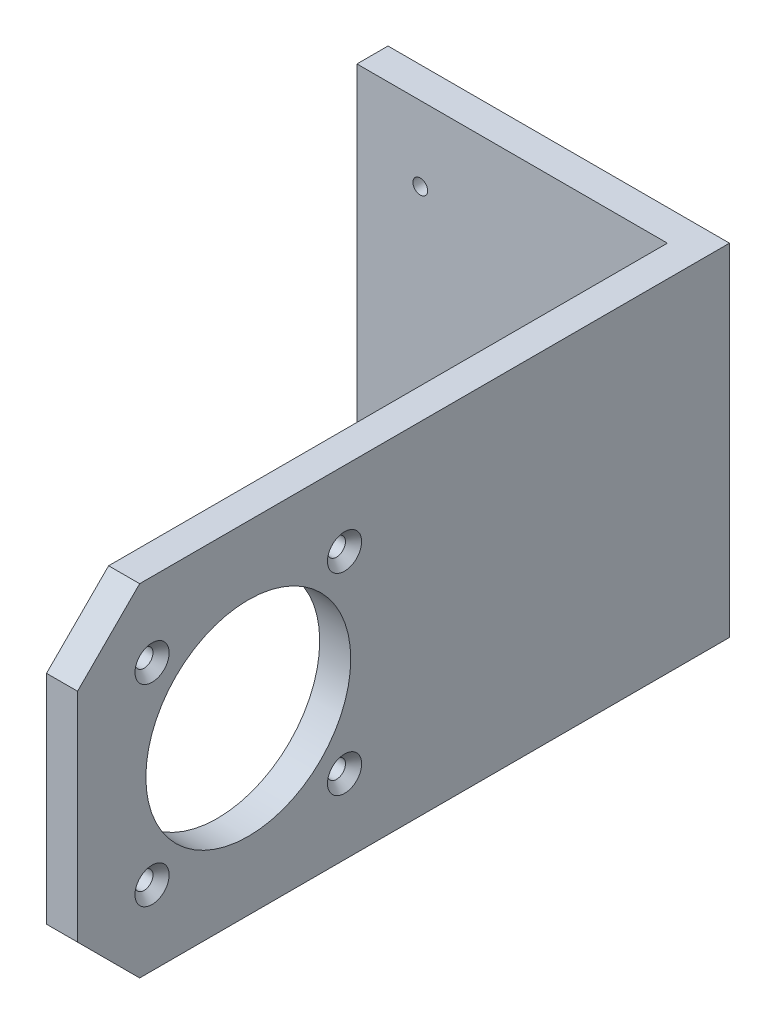
SolidWorks part; units mm, degrees
ref_plane "Ön Düzlem" through (0, 0, 0) normal (0, 0, 1) x (1, 0, 0)
ref_plane "Üst Düzlem" through (0, 0, 0) normal (0, 1, 0) x (1, 0, 0)
ref_plane "Sağ Düzlem" through (0, 0, 0) normal (1, 0, 0) x (0, 0, -1)
sketch "Sketch1" plane through (0, 0, 0) normal (0, 0, 1) x (1, 0, 0)
  line L1 (-27.5, 27.5) -> (27.5, 27.5)
  line L2 (-27.5, 27.5) -> (-27.5, -27.5)
  line L3 (-27.5, -27.5) -> (27.5, -27.5)
  line L4 (27.5, 27.5) -> (27.5, -27.5)
  line L5 (-27.5, 27.5) -> (27.5, -27.5) construction
  line L6 (-27.5, -27.5) -> (27.5, 27.5) construction
  point P0 (0, 0)
  dimension "D1" = 55
  dimension "D2" = 55
extrude "Boss-Extrude1" add sketch "Sketch1" along normal blind 5
sketch "Sketch2" plane through (0, 0, 5) normal (0, 0, 1) x (1, 0, 0)
  line L0 (-27.5, -27.5) -> (27.5, -27.5) construction
  line L1 (27.5, 27.5) -> (22.5, 27.5)
  line L2 (27.5, 27.5) -> (27.5, -27.5)
  line L3 (27.5, -27.5) -> (22.5, -27.5)
  line L4 (22.5, 27.5) -> (22.5, -27.5)
  dimension "D1" = 5
extrude "Boss-Extrude2" add sketch "Sketch2" along normal blind 100
sketch "Sketch3" plane through (27.5, 0, 0) normal (1, 0, 0) x (0, 0, -1)
  line L0 (-105, -27.5) -> (-105, 27.5) construction
  circle A0 centre (-77.5, 0) radius 16.5
  point P2 (-105, 0)
  dimension "D1" = 33
  dimension "D2" = 27.5
extrude "Cut-Extrude1" cut sketch "Sketch3" against normal up to next
sketch "Sketch4" plane through (0, 0, 5) normal (0, 0, 1) x (1, 0, 0)
  circle A0 centre (0, 0) radius 2.5
  dimension "D1" = 5
extrude "Cut-Extrude2" cut sketch "Sketch4" against normal up to next
sketch "Sketch5" plane through (27.5, 0, 0) normal (1, 0, 0) x (0, 0, -1)
  line L0 (-105, 27.5) -> (-95, 27.5)
  line L1 (-105, 27.5) -> (0, 27.5) construction
  line L2 (-95, 27.5) -> (-105, 17.5)
  line L3 (-105, -27.5) -> (-105, 27.5) construction
  line L4 (-105, 17.5) -> (-105, 27.5)
  line L5 (-105, -27.5) -> (-95, -27.5)
  line L6 (-105, -27.5) -> (0, -27.5) construction
  line L7 (-95, -27.5) -> (-105, -17.5)
  line L8 (-105, -17.5) -> (-105, -27.5)
  dimension "D1" = 45
  dimension "D2" = 10
  dimension "D3" = 10
extrude "Cut-Extrude3" cut sketch "Sketch5" against normal up to next
hole_wizard "#4-48 Tapped Hole1" positions "Sketch7" profile "Sketch6" tap size "#4-48" standard "ANSI Inch"
sketch "Sketch7" plane through (0, 0, 5) normal (0, 0, 1) x (1, 0, 0)
  point P0 (-17.3, 15.5)
  point P3 (-17.3, -15.5)
sketch "Sketch6" plane through (-17.3, 15.5, 5) normal (1, 0, 0) x (0, -1, 0)
  line L0 (0, 0) -> (0, 4.2135)
  line L1 (0, 4.2135) -> (1.1874, 3.5)
  line L2 (1.1874, 3.5) -> (1.1874, 0)
  line L5 (1.1874, 0) -> (0, 0)
  line L10 (0, 4.2135) -> (-1.1875, 3.5) construction
  line L11 (0, -6.35) -> (0, 107.95) construction
  dimension "Tap Drill Dia." = 2.3749
  dimension "Tap Drill Depth" = 3.5
  dimension "Drill Angle" = 118
hole_wizard "CSK for M2.5 Flat Head Machine Screw1" positions "Sketch9" profile "Sketch8" countersink size "M2.5" standard "ANSI Metric" end condition up to next
sketch "Sketch9" plane through (27.5, 0, 0) normal (1, 0, 0) x (0, 0, -1)
  point P2 (-93, 15.5)
  point P5 (-62, 15.5)
  point P8 (-62, -15.5)
  point P11 (-93, -15.5)
sketch "Sketch8" plane through (27.5, 15.5, 93) normal (0, 1, 0) x (0, 0, -1)
  line L0 (0, 0) -> (0, 5)
  line L1 (0, 5) -> (1.45, 5)
  line L2 (1.45, 5) -> (1.45, 1.3)
  line L3 (1.45, 1.3) -> (2.75, 0)
  line L5 (2.75, 0) -> (0, 0)
  line L6 (-1.45, 1.3) -> (-2.75, 0) construction
  line L11 (0, -6.35) -> (0, 107.95) construction
  dimension "Thru Hole Dia." = 2.9
  dimension "Thru Hole Depth" = 5
  dimension "Near C'Sink Dia." = 5.5
  dimension "Near C'Sink Angle" = 90
